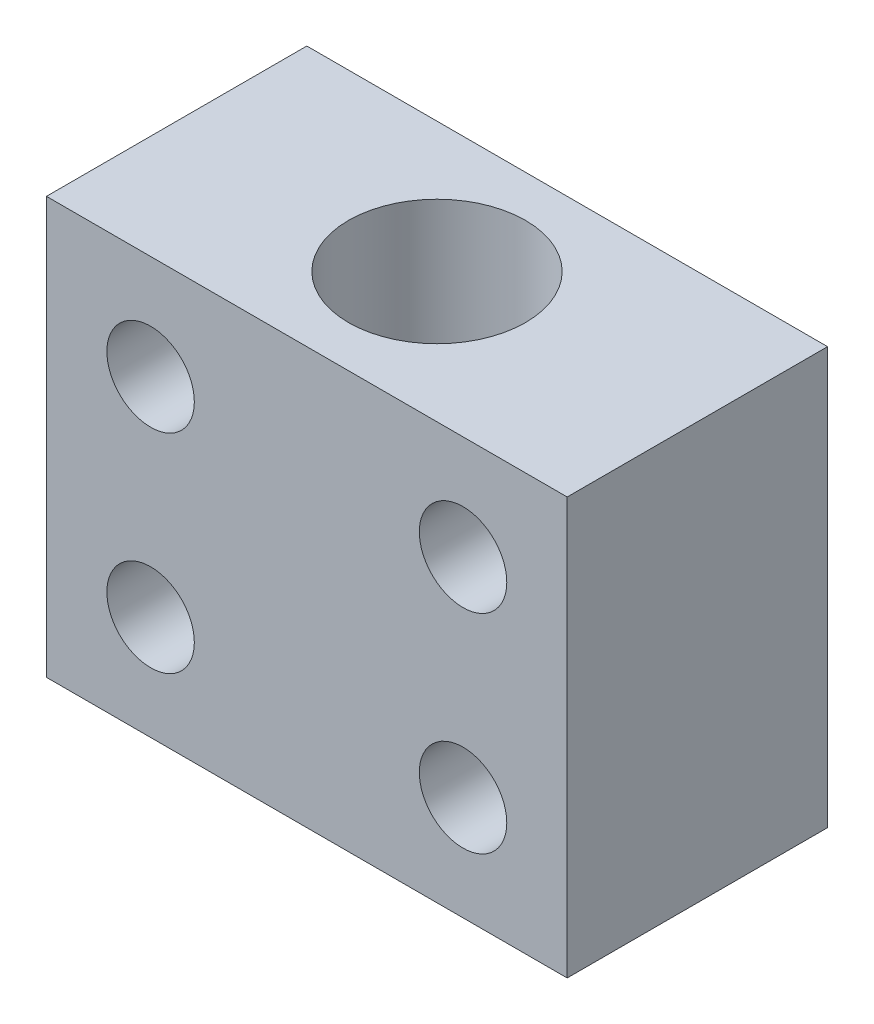
SolidWorks part; units mm, degrees
material "1.7225 (42CrMo4)"
ref_plane "Alzado" through (0, 0, 0) normal (0, 0, 1) x (1, 0, 0)
ref_plane "Planta" through (0, 0, 0) normal (0, 1, 0) x (1, 0, 0)
ref_plane "Vista lateral" through (0, 0, 0) normal (1, 0, 0) x (0, 0, -1)
sketch "Croquis1" plane through (0, 0, 0) normal (0, 0, 1) x (1, 0, 0)
  line L1 (-25, -20) -> (25, -20)
  line L2 (-25, -20) -> (-25, 20)
  line L3 (-25, 20) -> (25, 20)
  line L4 (25, -20) -> (25, 20)
  line L5 (-25, -20) -> (25, 20) construction
  line L6 (-25, 20) -> (25, -20) construction
  point P0 (0, 0)
  dimension "D1" = 40
  dimension "D2" = 50
extrude "Saliente-Extruir1" add sketch "Croquis1" along normal mid plane 25
hole_wizard "Taladro de margen para M81" positions "Croquis2" profile "Croquis3" hole size "M8" standard "ISO" end condition through all
sketch "Croquis2" plane through (0, 0, 12.5) normal (0, 0, 1) x (1, 0, 0)
  line L1 (15, -10) -> (-15, -10) construction
  line L2 (15, -10) -> (15, 10) construction
  line L3 (15, 10) -> (-15, 10) construction
  line L4 (-15, -10) -> (-15, 10) construction
  line L5 (15, -10) -> (-15, 10) construction
  line L6 (15, 10) -> (-15, -10) construction
  point P0 (-15, 10)
  point P75 (-15, -10)
  point P78 (15, -10)
  point P81 (15, 10)
  dimension "D1" = 30
  dimension "D2" = 20
sketch "Croquis3" plane through (-15, 10, 12.5) normal (1, 0, 0) x (0, -1, 0)
  line L0 (0, 0) -> (0, 25)
  line L1 (0, 25) -> (4.2, 25)
  line L2 (4.2, 25) -> (4.2, 0)
  line L5 (4.2, 0) -> (0, 0)
  line L11 (0, -6.35) -> (0, 107.95) construction
  dimension "Diámetro de taladro hasta el siguiente" = 8.4
  dimension "Profundidad de taladro hasta el siguiente" = 25
hole_wizard "Taladro de margen para M161" positions "Croquis4" profile "Croquis5" hole size "M16" standard "ISO" end condition through all
sketch "Croquis4" plane through (0, 20, 0) normal (0, 1, 0) x (1, 0, 0)
  point P0 (0, 0)
sketch "Croquis5" plane through (0, 20, 0) normal (1, 0, 0) x (0, 0, 1)
  line L0 (0, 0) -> (0, 40)
  line L1 (0, 40) -> (8.5, 40)
  line L2 (8.5, 40) -> (8.5, 0)
  line L5 (8.5, 0) -> (0, 0)
  line L11 (0, -6.35) -> (0, 107.95) construction
  dimension "Diámetro de taladro hasta el siguiente" = 17
  dimension "Profundidad de taladro hasta el siguiente" = 40
